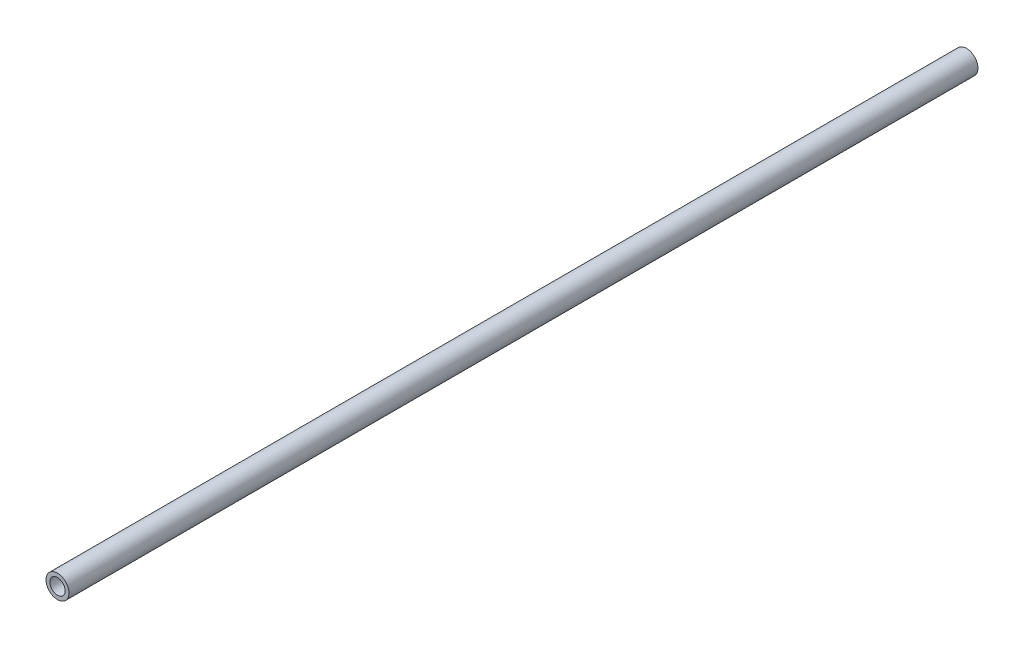
SolidWorks part; units mm, degrees
ref_plane "Płaszczyzna przednia" through (0, 0, 0) normal (0, 0, 1) x (1, 0, 0)
ref_plane "Płaszczyzna górna" through (0, 0, 0) normal (0, 1, 0) x (1, 0, 0)
ref_plane "Płaszczyzna prawa" through (0, 0, 0) normal (1, 0, 0) x (0, 0, -1)
sketch "Szkic1" plane through (0, 0, 0) normal (0, 0, 1) x (1, 0, 0)
  circle A0 centre (0, 0) radius 12
  circle A1 centre (0, 0) radius 8
  dimension "D1" = 16
  dimension "D2" = 24
extrude "Dodanie-wyciągnięcie1" add sketch "Szkic1" along normal blind 948
cosmetic thread "Oznaczenie gwintu1" parameters "D1"=24, "D2"=21.797
cosmetic thread "Oznaczenie gwintu2" parameters "D1"=5, "D2"=20.704
